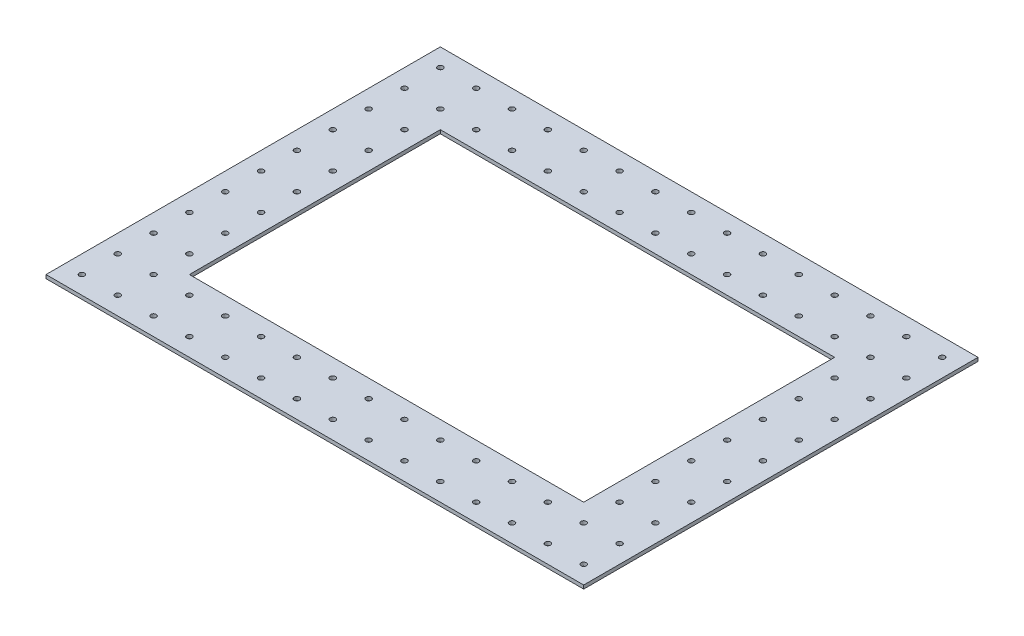
SolidWorks part; units mm, degrees
ref_plane "Front Plane" through (0, 0, 0) normal (0, 0, 1) x (1, 0, 0)
ref_plane "Top Plane" through (0, 0, 0) normal (0, 1, 0) x (1, 0, 0)
ref_plane "Right Plane" through (0, 0, 0) normal (1, 0, 0) x (0, 0, -1)
sketch "Sketch1" plane through (0, 0, 0) normal (1, 0, 0) x (0, 0, -1)
  line L0 (-26.6783, 0) -> (193.3217, 0)
  line L1 (55, 0) -> (-55, 0) construction
  line L2 (-26.6783, 0) -> (-26.6783, 2)
  line L3 (193.3217, 0) -> (193.3217, 2)
  line L4 (193.3217, 2) -> (-26.6783, 2)
  dimension "D1" = 220
  dimension "D2" = 2
extrude "Boss-Extrude1" add sketch "Sketch1" along normal blind 300 contours L4 L2 L0 L3
sketch "Sketch2" plane through (0, 2, 0) normal (0, 1, 0) x (1, 0, 0)
  line L0 (0, -1.1) -> (0, 1.1) construction
  line L5 (40, 153.3217) -> (260, 153.3217)
  line L20 (300, 193.3217) -> (0, 193.3217) construction
  line L24 (300, -26.6783) -> (0, -26.6783) construction
  line L52 (300, 193.3217) -> (300, -26.6783) construction
  line L83 (260, 153.3217) -> (260, 13.3217)
  line L86 (10, 3.3217) -> (23.6131, 3.3217) construction
  line L90 (30, -16.6783) -> (30, -3.7972) construction
  line L91 (40, 153.3217) -> (40, 13.3217)
  line L93 (40, 13.3217) -> (260, 13.3217)
  circle A23 centre (10, -16.6783) radius 1.5
  circle A24 centre (30, -16.6783) radius 1.5
  circle A25 centre (50, -16.6783) radius 1.5
  circle A26 centre (70, -16.6783) radius 1.5
  circle A27 centre (90, -16.6783) radius 1.5
  circle A28 centre (110, -16.6783) radius 1.5
  circle A29 centre (130, -16.6783) radius 1.5
  circle A30 centre (150, -16.6783) radius 1.5
  circle A31 centre (170, -16.6783) radius 1.5
  circle A32 centre (190, -16.6783) radius 1.5
  circle A33 centre (210, -16.6783) radius 1.5
  circle A34 centre (230, -16.6783) radius 1.5
  circle A35 centre (250, -16.6783) radius 1.5
  circle A36 centre (270, -16.6783) radius 1.5
  circle A37 centre (290, -16.6783) radius 1.5
  circle A38 centre (10, 3.3217) radius 1.5
  circle A51 centre (270, 3.3217) radius 1.5
  circle A52 centre (290, 3.3217) radius 1.5
  circle A53 centre (10, 23.3217) radius 1.5
  circle A54 centre (30, 23.3217) radius 1.5
  circle A66 centre (270, 23.3217) radius 1.5
  circle A67 centre (290, 23.3217) radius 1.5
  circle A68 centre (10, 43.3217) radius 1.5
  circle A69 centre (30, 43.3217) radius 1.5
  circle A81 centre (270, 43.3217) radius 1.5
  circle A82 centre (290, 43.3217) radius 1.5
  circle A83 centre (10, 63.3217) radius 1.5
  circle A84 centre (30, 63.3217) radius 1.5
  circle A96 centre (270, 63.3217) radius 1.5
  circle A97 centre (290, 63.3217) radius 1.5
  circle A98 centre (10, 83.3217) radius 1.5
  circle A99 centre (30, 83.3217) radius 1.5
  circle A111 centre (270, 83.3217) radius 1.5
  circle A112 centre (290, 83.3217) radius 1.5
  circle A113 centre (10, 103.3217) radius 1.5
  circle A114 centre (30, 103.3217) radius 1.5
  circle A126 centre (270, 103.3217) radius 1.5
  circle A127 centre (290, 103.3217) radius 1.5
  circle A128 centre (10, 123.3217) radius 1.5
  circle A129 centre (30, 123.3217) radius 1.5
  circle A141 centre (270, 123.3217) radius 1.5
  circle A142 centre (290, 123.3217) radius 1.5
  circle A143 centre (10, 143.3217) radius 1.5
  circle A144 centre (30, 143.3217) radius 1.5
  circle A156 centre (270, 143.3217) radius 1.5
  circle A157 centre (290, 143.3217) radius 1.5
  circle A158 centre (10, 163.3217) radius 1.5
  circle A159 centre (30, 163.3217) radius 1.5
  circle A172 centre (290, 163.3217) radius 1.5
  circle A173 centre (10, 183.3217) radius 1.5
  circle A174 centre (30, 183.3217) radius 1.5
  circle A175 centre (50, 183.3217) radius 1.5
  circle A176 centre (70, 183.3217) radius 1.5
  circle A177 centre (90, 183.3217) radius 1.5
  circle A178 centre (110, 183.3217) radius 1.5
  circle A179 centre (130, 183.3217) radius 1.5
  circle A180 centre (150, 183.3217) radius 1.5
  circle A181 centre (170, 183.3217) radius 1.5
  circle A182 centre (190, 183.3217) radius 1.5
  circle A183 centre (210, 183.3217) radius 1.5
  circle A184 centre (230, 183.3217) radius 1.5
  circle A185 centre (250, 183.3217) radius 1.5
  circle A186 centre (270, 183.3217) radius 1.5
  circle A187 centre (290, 183.3217) radius 1.5
  circle A188 centre (50, 163.3217) radius 1.5 [skipped]
  circle A189 centre (70, 163.3217) radius 1.5 [skipped]
  circle A190 centre (90, 163.3217) radius 1.5 [skipped]
  circle A191 centre (110, 163.3217) radius 1.5 [skipped]
  circle A192 centre (130, 163.3217) radius 1.5 [skipped]
  circle A193 centre (150, 163.3217) radius 1.5 [skipped]
  circle A194 centre (170, 163.3217) radius 1.5 [skipped]
  circle A195 centre (190, 163.3217) radius 1.5 [skipped]
  circle A196 centre (210, 163.3217) radius 1.5 [skipped]
  circle A197 centre (230, 163.3217) radius 1.5 [skipped]
  circle A198 centre (250, 163.3217) radius 1.5 [skipped]
  circle A199 centre (30, 3.3217) radius 1.5 [skipped]
  circle A200 centre (50, 143.3217) radius 1.5 [skipped]
  circle A201 centre (50, 123.3217) radius 1.5 [skipped]
  circle A202 centre (50, 103.3217) radius 1.5 [skipped]
  circle A203 centre (50, 83.3217) radius 1.5 [skipped]
  circle A204 centre (50, 63.3217) radius 1.5 [skipped]
  circle A205 centre (50, 43.3217) radius 1.5 [skipped]
  circle A206 centre (50, 23.3217) radius 1.5 [skipped]
  circle A207 centre (70, 143.3217) radius 1.5 [skipped]
  circle A208 centre (90, 143.3217) radius 1.5 [skipped]
  circle A209 centre (130, 143.3217) radius 1.5 [skipped]
  circle A210 centre (110, 143.3217) radius 1.5 [skipped]
  circle A211 centre (150, 143.3217) radius 1.5 [skipped]
  circle A212 centre (190, 143.3217) radius 1.5 [skipped]
  circle A213 centre (170, 143.3217) radius 1.5 [skipped]
  circle A214 centre (170, 123.3217) radius 1.5 [skipped]
  circle A215 centre (170, 103.3217) radius 1.5 [skipped]
  circle A216 centre (170, 83.3217) radius 1.5 [skipped]
  circle A217 centre (170, 63.3217) radius 1.5 [skipped]
  circle A218 centre (170, 43.3217) radius 1.5 [skipped]
  circle A219 centre (170, 23.3217) radius 1.5 [skipped]
  circle A220 centre (150, 123.3217) radius 1.5 [skipped]
  circle A221 centre (150, 103.3217) radius 1.5 [skipped]
  circle A222 centre (150, 63.3217) radius 1.5 [skipped]
  circle A223 centre (150, 83.3217) radius 1.5 [skipped]
  circle A224 centre (150, 43.3217) radius 1.5 [skipped]
  circle A225 centre (150, 23.3217) radius 1.5 [skipped]
  circle A226 centre (130, 123.3217) radius 1.5 [skipped]
  circle A227 centre (130, 63.3217) radius 1.5 [skipped]
  circle A228 centre (130, 43.3217) radius 1.5 [skipped]
  circle A229 centre (130, 23.3217) radius 1.5 [skipped]
  circle A230 centre (130, 83.3217) radius 1.5 [skipped]
  circle A231 centre (130, 103.3217) radius 1.5 [skipped]
  circle A232 centre (110, 123.3217) radius 1.5 [skipped]
  circle A233 centre (110, 103.3217) radius 1.5 [skipped]
  circle A234 centre (110, 83.3217) radius 1.5 [skipped]
  circle A235 centre (110, 63.3217) radius 1.5 [skipped]
  circle A236 centre (110, 43.3217) radius 1.5 [skipped]
  circle A237 centre (110, 23.3217) radius 1.5 [skipped]
  circle A238 centre (90, 23.3217) radius 1.5 [skipped]
  circle A239 centre (90, 43.3217) radius 1.5 [skipped]
  circle A240 centre (90, 63.3217) radius 1.5 [skipped]
  circle A241 centre (90, 83.3217) radius 1.5 [skipped]
  circle A242 centre (90, 103.3217) radius 1.5 [skipped]
  circle A243 centre (90, 123.3217) radius 1.5 [skipped]
  circle A244 centre (70, 123.3217) radius 1.5 [skipped]
  circle A245 centre (70, 103.3217) radius 1.5 [skipped]
  circle A246 centre (70, 83.3217) radius 1.5 [skipped]
  circle A247 centre (70, 43.3217) radius 1.5 [skipped]
  circle A248 centre (70, 63.3217) radius 1.5 [skipped]
  circle A249 centre (70, 23.3217) radius 1.5 [skipped]
  arc A250 (251.5, 3.3217) -> (248.5, 3.3217) centre (250, 3.3217) ccw [skipped]
  arc A251 (231.5, 3.3217) -> (228.5, 3.3217) centre (230, 3.3217) ccw [skipped]
  arc A252 (211.5, 3.3217) -> (208.5, 3.3217) centre (210, 3.3217) ccw [skipped]
  arc A253 (191.5, 3.3217) -> (188.5, 3.3217) centre (190, 3.3217) ccw [skipped]
  arc A254 (171.5, 3.3217) -> (168.5, 3.3217) centre (170, 3.3217) ccw [skipped]
  arc A255 (151.5, 3.3217) -> (148.5, 3.3217) centre (150, 3.3217) ccw [skipped]
  arc A256 (131.5, 3.3217) -> (128.5, 3.3217) centre (130, 3.3217) ccw [skipped]
  arc A257 (111.5, 3.3217) -> (108.5, 3.3217) centre (110, 3.3217) ccw [skipped]
  arc A258 (91.5, 3.3217) -> (88.5, 3.3217) centre (90, 3.3217) ccw [skipped]
  arc A259 (71.5, 3.3217) -> (68.5, 3.3217) centre (70, 3.3217) ccw [skipped]
  arc A260 (51.5, 3.3217) -> (48.5, 3.3217) centre (50, 3.3217) ccw [skipped]
  circle A261 centre (190, 123.3217) radius 1.5 [skipped]
  circle A262 centre (190, 103.3217) radius 1.5 [skipped]
  circle A263 centre (190, 83.3217) radius 1.5 [skipped]
  circle A264 centre (190, 43.3217) radius 1.5 [skipped]
  circle A265 centre (190, 23.3217) radius 1.5 [skipped]
  circle A266 centre (190, 63.3217) radius 1.5 [skipped]
  circle A267 centre (210, 23.3217) radius 1.5 [skipped]
  circle A268 centre (210, 43.3217) radius 1.5 [skipped]
  circle A269 centre (210, 63.3217) radius 1.5 [skipped]
  circle A270 centre (210, 83.3217) radius 1.5 [skipped]
  circle A271 centre (210, 103.3217) radius 1.5 [skipped]
  circle A272 centre (210, 123.3217) radius 1.5 [skipped]
  circle A273 centre (210, 143.3217) radius 1.5 [skipped]
  circle A274 centre (230, 143.3217) radius 1.5 [skipped]
  circle A275 centre (230, 123.3217) radius 1.5 [skipped]
  circle A276 centre (230, 103.3217) radius 1.5 [skipped]
  circle A277 centre (230, 83.3217) radius 1.5 [skipped]
  circle A278 centre (230, 63.3217) radius 1.5 [skipped]
  circle A279 centre (230, 43.3217) radius 1.5 [skipped]
  circle A280 centre (230, 23.3217) radius 1.5 [skipped]
  circle A281 centre (250, 23.3217) radius 1.5 [skipped]
  circle A282 centre (250, 63.3217) radius 1.5 [skipped]
  circle A283 centre (250, 43.3217) radius 1.5 [skipped]
  circle A284 centre (250, 83.3217) radius 1.5 [skipped]
  circle A285 centre (250, 103.3217) radius 1.5 [skipped]
  circle A286 centre (250, 143.3217) radius 1.5 [skipped]
  circle A287 centre (250, 123.3217) radius 1.5 [skipped]
  circle A288 centre (50, 163.3217) radius 1.5
  circle A289 centre (70, 163.3217) radius 1.5
  circle A290 centre (90, 163.3217) radius 1.5
  circle A291 centre (110, 163.3217) radius 1.5
  circle A292 centre (130, 163.3217) radius 1.5
  circle A293 centre (150, 163.3217) radius 1.5
  circle A294 centre (170, 163.3217) radius 1.5
  circle A295 centre (190, 163.3217) radius 1.5
  circle A296 centre (210, 163.3217) radius 1.5
  circle A297 centre (230, 163.3217) radius 1.5
  circle A298 centre (250, 163.3217) radius 1.5
  circle A300 centre (30, 3.3217) radius 1.5
  circle A301 centre (50, 3.3217) radius 1.5
  circle A302 centre (70, 3.3217) radius 1.5
  circle A303 centre (90, 3.3217) radius 1.5
  circle A304 centre (110, 3.3217) radius 1.5
  circle A305 centre (130, 3.3217) radius 1.5
  circle A306 centre (150, 3.3217) radius 1.5
  circle A307 centre (170, 3.3217) radius 1.5
  circle A308 centre (190, 3.3217) radius 1.5
  circle A309 centre (210, 3.3217) radius 1.5
  circle A310 centre (230, 3.3217) radius 1.5
  circle A311 centre (250, 3.3217) radius 1.5
  circle A312 centre (270, 163.3217) radius 1.5 [skipped]
  circle A313 centre (270, 163.3217) radius 1.5 [skipped]
  circle A314 centre (270, 163.3217) radius 1.5
  dimension "D9" = 40
  dimension "D11" = 40
  dimension "D38" = 3
  dimension "D5" = 20
  dimension "D7" = 11
  dimension "D2" = 10
  dimension "D4" = 20
  dimension "D6" = 15
  dimension "D8" = 2
  dimension "D12" = 13
  dimension "D13" = 13
  dimension "D39" = 10
extrude "Cut-Extrude1" cut sketch "Sketch2" against normal blind 10
